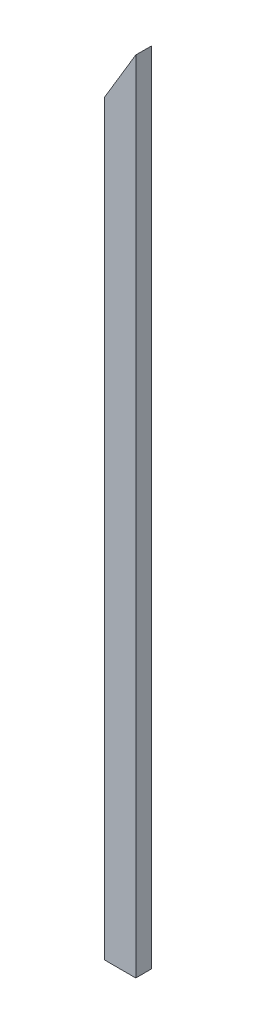
SolidWorks part; units mm, degrees
material "Cedar"
ref_plane "Front Plane" through (0, 0, 0) normal (0, 0, 1) x (1, 0, 0)
ref_plane "Top Plane" through (0, 0, 0) normal (0, 1, 0) x (1, 0, 0)
ref_plane "Right Plane" through (0, 0, 0) normal (1, 0, 0) x (0, 0, -1)
sketch "Sketch1" plane through (0, 0, 0) normal (0, 0, 1) x (1, 0, 0)
  line L1 (-295.0184, 474.8107) -> (-256.9184, 474.8107)
  line L2 (-295.0184, 474.8107) -> (-295.0184, -505.6039)
  line L3 (-295.0184, -505.6039) -> (-256.9184, -505.6039)
  line L4 (-256.9184, 474.8107) -> (-256.9184, -505.6039)
  dimension "D1" = 980.4146
  dimension "D2" = 38.1
extrude "Boss-Extrude1" add sketch "Sketch1" along normal blind 19.05
sketch "Sketch2" plane through (0, 0, 19.05) normal (0, 0, 1) x (1, 0, 0)
  line L0 (-295.0184, 411.1503) -> (-256.9184, 474.8107)
  line L1 (-295.0184, 474.8107) -> (-295.0184, -505.6039) construction
  line L2 (-256.9184, 474.8107) -> (-295.0184, 474.8107)
  line L3 (-295.0184, 474.8107) -> (-295.0184, 411.1503)
  line L4 (-256.9184, -505.6039) -> (-256.9184, 474.8107) construction
  dimension "D1" = 30.9
extrude "Cut-Extrude1" cut sketch "Sketch2" against normal through all
